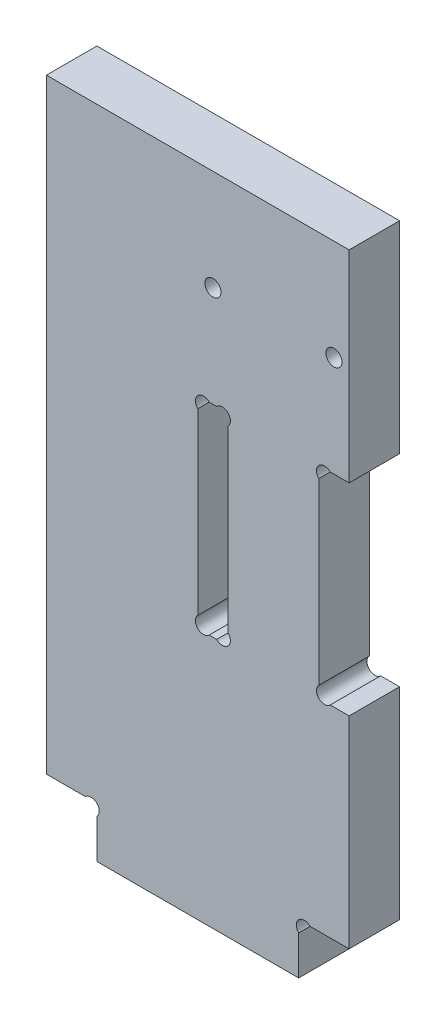
SolidWorks part; units mm, degrees
ref_plane "Plan de face" through (0, 0, 0) normal (0, 0, 1) x (1, 0, 0)
ref_plane "Plan de dessus" through (0, 0, 0) normal (0, 1, 0) x (1, 0, 0)
ref_plane "Plan de droite" through (0, 0, 0) normal (1, 0, 0) x (0, 0, -1)
sketch "Esquisse1" plane through (0, 0, 0) normal (0, 0, 1) x (1, 0, 0)
  line L0 (-81.6515, 0) -> (336.943, 0) construction
  line L2 (330, 201.3745) -> (330, -7.0046) construction
  line L3 (336.943, 130) -> (-81.6515, 130) construction
  line L4 (324, 147.7086) -> (324, 30.1101) construction
  line L6 (-24.2523, 10) -> (336.943, 10) construction
  line L7 (300, 30.1101) -> (300, 175.7082) construction
  line L8 (306, 30.1101) -> (306, 147.7086) construction
  line L9 (315, 159.3669) -> (315, 107.5758) construction
  line L10 (-50.8519, 70) -> (336.943, 70) construction
  line L12 (303, 82.1628) -> (303, 52.0341) construction
  line L13 (-50.8519, 50) -> (331.3802, 50) construction
  line L14 (306, 50) -> (292.3754, 63.6246) construction
  line L15 (302.2627, 50) -> (303.7373, 50)
  line L16 (326.2627, 50) -> (330, 50)
  line L17 (326.2627, 90) -> (330, 90)
  line L18 (302.2627, 90) -> (303.7373, 90)
  line L24 (-24.2523, 30) -> (370.2645, 30) construction
  line L31 (322.2627, 10) -> (330, 10)
  line L32 (320, 0) -> (280, 0)
  line L33 (280, 7.7373) -> (280, 0)
  line L34 (320, 7.7373) -> (320, 0)
  line L35 (280, -28.8) -> (280, 19.4852) construction
  line L36 (270, 130) -> (270, 10)
  line L39 (324, 87.7373) -> (324, 52.2627)
  line L40 (306, 52.2627) -> (306, 87.7373)
  line L41 (300, 87.7373) -> (300, 52.2627)
  line L42 (330, 10) -> (330, 50)
  line L43 (330, 90) -> (330, 130)
  line L44 (330, 130) -> (270, 130)
  line L49 (270, 10) -> (277.7373, 10)
  line L50 (327, 35.3379) -> (327, 19.4852) construction
  line L51 (270, 201.3745) -> (270, -7.0046) construction
  arc A0 (303.7373, 50) -> (306, 52.2627) centre (304.8686, 51.1314) ccw
  arc A1 (302.2627, 50) -> (300, 52.2627) centre (301.1314, 51.1314) cw
  arc A2 (303.7373, 90) -> (306, 87.7373) centre (304.8686, 88.8686) cw
  arc A3 (302.2627, 90) -> (300, 87.7373) centre (301.1314, 88.8686) ccw
  arc A4 (326.2627, 50) -> (324, 52.2627) centre (325.1314, 51.1314) cw
  arc A5 (326.2627, 90) -> (324, 87.7373) centre (325.1314, 88.8686) ccw
  arc A12 (280, 7.7373) -> (277.7373, 10) centre (278.8686, 8.8686) ccw
  arc A13 (320, 7.7373) -> (322.2627, 10) centre (321.1314, 8.8686) cw
  circle A17 centre (327, 110) radius 1.6
  circle A18 centre (303, 110) radius 1.6
  dimension "D19" = 60
  dimension "D2" = 130
  dimension "D3" = 60
  dimension "D5" = 15
  dimension "D6" = 6
  dimension "D7" = 6
  dimension "D8" = 30
  dimension "D11" = 3
  dimension "D12" = 20
  dimension "D13" = 45
  dimension "D20" = 3
extrude "Extrusion1" add sketch "Esquisse1" along normal blind 10
